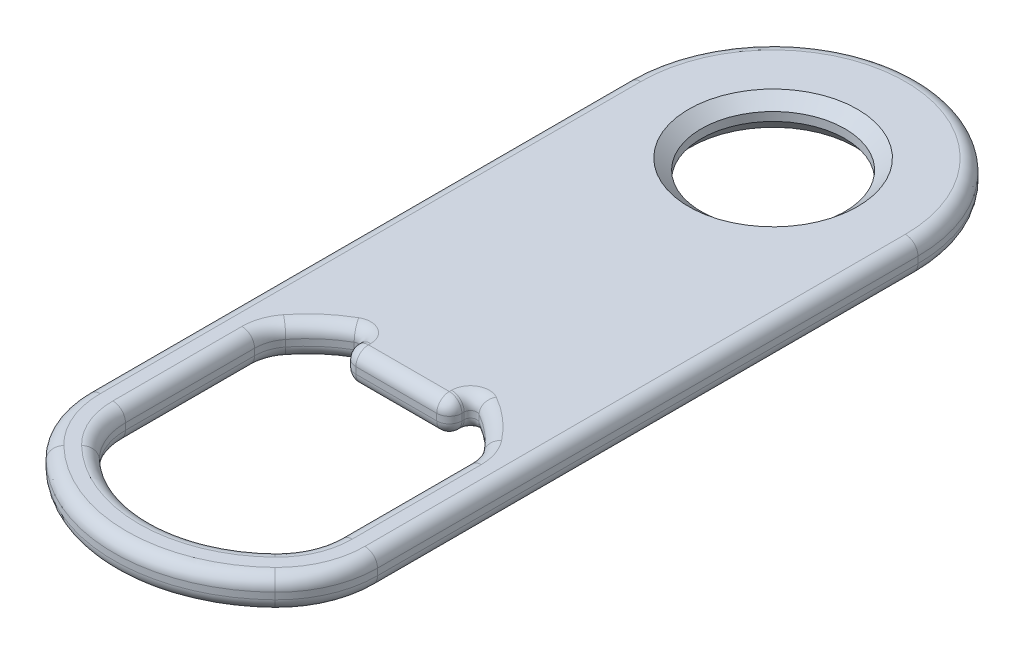
SolidWorks part; units mm, degrees
ref_plane "Front Plane" through (0, 0, 0) normal (0, 0, 1) x (1, 0, 0)
ref_plane "Top Plane" through (0, 0, 0) normal (0, 1, 0) x (1, 0, 0)
ref_plane "Right Plane" through (0, 0, 0) normal (1, 0, 0) x (0, 0, -1)
sketch "Sketch2" plane through (0, 0, 0) normal (1, 0, 0) x (0, 0, -1)
  line L1 (6.5, 3) -> (-6.5, 3) construction
  line L3 (6.5, 11.24) -> (-6.5, 11.24)
  line L5 (10.5, 11.24) -> (0, 11.24) construction
ref_plane "Plane1" through (0, 11.24, 0) normal (0, -1, 0) x (0, 0, 1)
sketch "Sketch3" plane through (0, 11.24, 0) normal (0, -1, 0) x (0, 0, 1)
  line L0 (-5.7, 0) -> (-12, 0)
  line L6 (49.3226, 0) -> (52.3226, 0)
  line L10 (0, 0) -> (0, 20.1636) construction
  line L14 (-12, 0) -> (-12, 11.5)
  line L15 (-12, 0) -> (52.3226, 0) construction
  line L19 (29.9066, 4.2079) -> (29.9066, 0)
  line L20 (27.9066, 4.2079) -> (29.9066, 4.2079)
  line L21 (31.7328, 8.5) -> (44.6183, 8.5)
  line L23 (-12, 11.5) -> (45.4063, 11.5)
  line L24 (5.7, 0) -> (29.9066, 0)
  circle A3 centre (0, 0) radius 5 construction
  arc A4 (5.7, 0) -> (-5.7, 0) centre (0, 0) ccw
  circle A6 centre (0, 0) radius 5.7 construction
  arc A7 (31.7328, 8.5) -> (27.9066, 4.2079) centre (36.9473, 0.0001) ccw
  arc A8 (44.6183, 8.5) -> (49.3226, 0) centre (39.2913, 0) cw
  arc A9 (45.4063, 11.5) -> (52.3226, 0) centre (39.3036, 0) cw
  dimension "D2" = 11.5
  dimension "D3" = 3
  dimension "D1" = 0.7
extrude "Boss-Extrude1" add sketch "Sketch3" against normal blind 2.52
sketch "Sketch5" plane through (0, 11.24, 0) normal (0, -1, 0) x (0, 0, 1)
  line L0 (45.4063, 11.5) -> (-12, 11.5) construction
  line L3 (0, 11.5) -> (0, 20.0815)
  line L4 (0, 20.0815) -> (-17.2066, 20.0815)
  line L5 (-17.2066, 20.0815) -> (-17.2066, -3.3259)
  line L6 (-17.2066, -3.3259) -> (-11.0086, -3.3259)
  arc A0 (0, 11.5) -> (-11.0086, -3.3259) centre (0, 0) ccw
  arc A1 (5.7, 0) -> (-5.7, 0) centre (0, 0) ccw construction
extrude "Cut-Extrude1" cut sketch "Sketch5" against normal blind 10
fillet "Fillet1" radius 1 1 edges at (-4.2079, 12.5, 29.9066)
fillet "Fillet2" radius 8 1 edges at (-11.5, 12.5, 45.4063)
fillet "Fillet3" radius 5 1 edges at (-8.5, 12.5, 44.6183)
fillet "Fillet4" radius 3 1 edges at (-8.5, 12.5, 31.7328)
fillet "Fillet5" radius 0.5 1 edges at (-4.2079, 12.5, 27.9066)
fillet "Fillet6" radius 1 8 edges at (-4.8997, 11.24, 51.3654) (-10.8699, 11.24, 46.0128) (-8.1317, 11.24, -8.1317) (-4.8997, 13.76, 51.3654) (-10.8699, 13.76, 46.0128) (-8.1317, 13.76, -8.1317) (-11.5, 11.24, 21.4504) (-11.5, 13.76, 21.4504)
fillet "Fillet7" radius 1 18 edges at (-3.7642, 11.24, 48.5895) (-8.1039, 11.24, 44.8562) (-8.5, 11.24, 37.7841) (-8.3372, 11.24, 31.6878) (-6.5346, 11.24, 29.4147) (-4.4571, 11.24, 28.2956) (-4.2079, 11.24, 28.8174) (-3.915, 11.24, 29.6137) (-3.7642, 13.76, 48.5895) (-8.1039, 13.76, 44.8562) (-8.5, 13.76, 37.7841) (-8.3372, 13.76, 31.6878) (-6.5346, 13.76, 29.4147) (-4.4571, 13.76, 28.2956) (-4.2079, 13.76, 28.8174) (-3.915, 13.76, 29.6137) (-1.6039, 11.24, 29.9066) (-1.6039, 13.76, 29.9066)
chamfer "Chamfer1" distance 1 angle 40 2 edges at (-5.7, 11.24, 0) (-5.7, 13.76, 0)
mirror "Mirror1" about plane through (0, 0, 0) normal (1, 0, 0) of bodies 104 101
